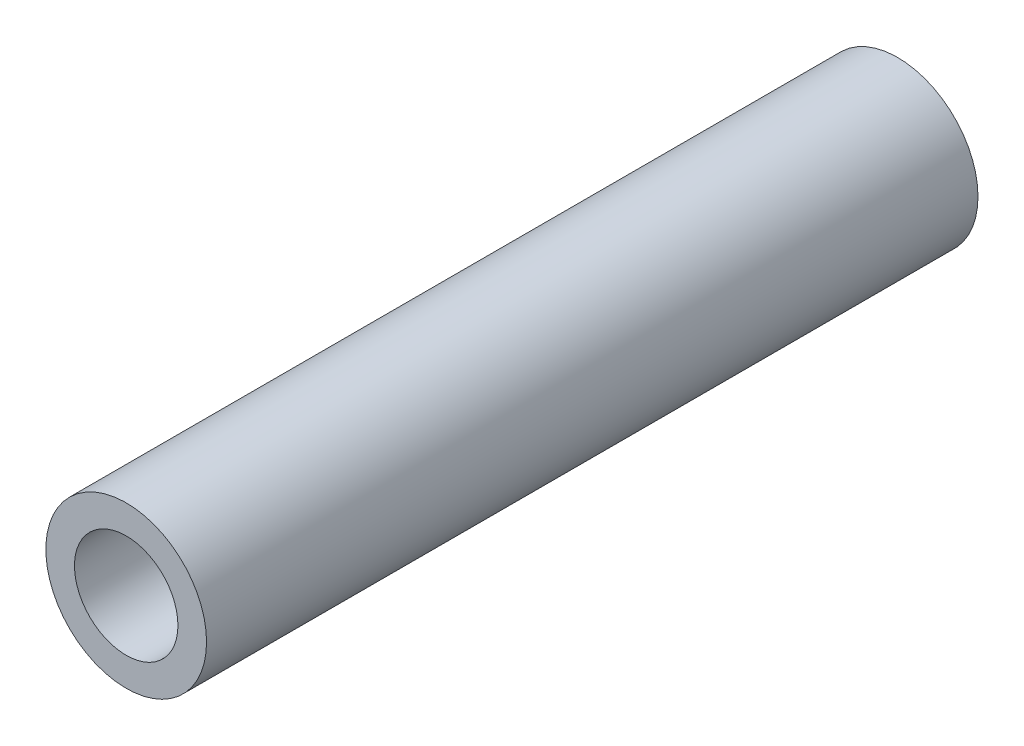
SolidWorks part; units mm, degrees
material "ABS"
ref_plane "Front Plane" through (0, 0, 0) normal (0, 0, 1) x (1, 0, 0)
ref_plane "Top Plane" through (0, 0, 0) normal (0, 1, 0) x (1, 0, 0)
ref_plane "Right Plane" through (0, 0, 0) normal (1, 0, 0) x (0, 0, -1)
sketch "Sketch1" plane through (0, 0, 0) normal (0, 0, 1) x (1, 0, 0)
  circle A0 centre (0, 0) radius 3.9688
  circle A1 centre (0, 0) radius 2.555
  dimension "D1" = 7.9375
  dimension "D2" = 5.11
extrude "Boss-Extrude1" add sketch "Sketch1" along normal blind 38.1
cosmetic thread "Cosmetic Thread1" parameters "D2"=6.35
